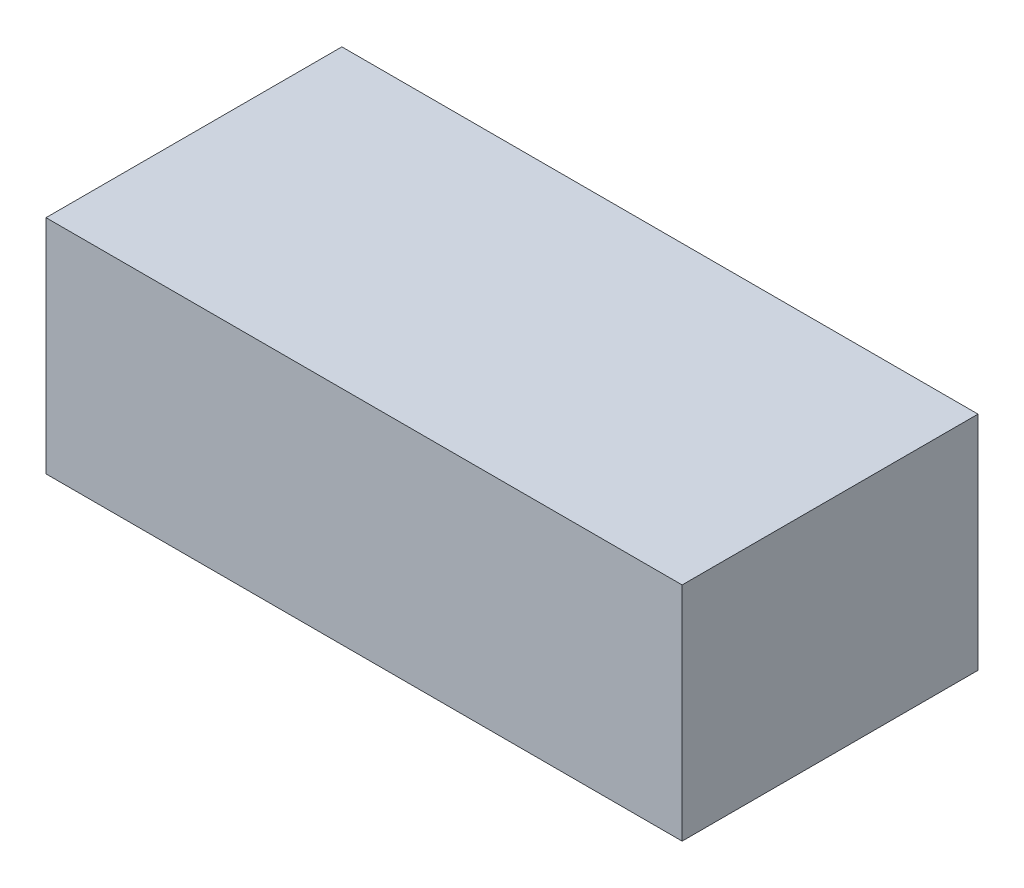
SolidWorks part; units mm, degrees
ref_plane "Front Plane" through (0, 0, 0) normal (0, 0, 1) x (1, 0, 0)
ref_plane "Top Plane" through (0, 0, 0) normal (0, 1, 0) x (1, 0, 0)
ref_plane "Right Plane" through (0, 0, 0) normal (1, 0, 0) x (0, 0, -1)
sketch "Sketch1" plane through (0, 0, 0) normal (0, 1, 0) x (1, 0, 0)
  line L1 (-21.5, 10) -> (21.5, 10)
  line L2 (-21.5, 10) -> (-21.5, -10)
  line L3 (-21.5, -10) -> (21.5, -10)
  line L4 (21.5, 10) -> (21.5, -10)
  line L5 (-21.5, 10) -> (21.5, -10) construction
  line L6 (-21.5, -10) -> (21.5, 10) construction
  point P0 (0, 0)
  dimension "D1" = 43
  dimension "D2" = 20
extrude "Boss-Extrude1" add sketch "Sketch1" along normal blind 15
